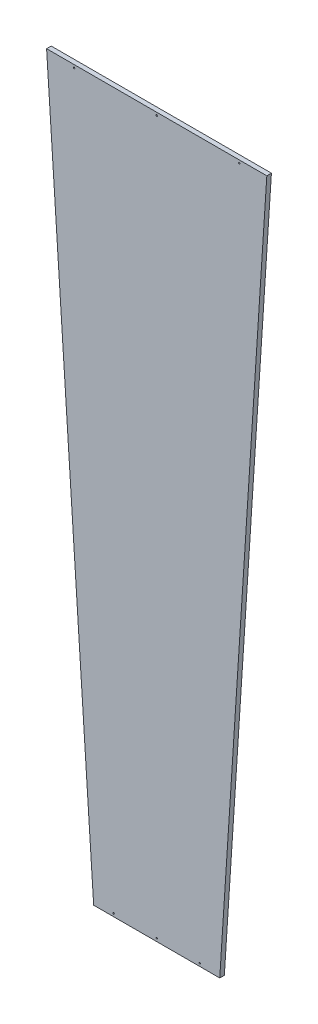
SolidWorks part; units mm, degrees
ref_plane "Plane1" through (0, 0, 0) normal (0, 0, 1) x (1, 0, 0)
ref_plane "Plane2" through (0, 0, 0) normal (0, 1, 0) x (1, 0, 0)
ref_plane "Plane3" through (0, 0, 0) normal (1, 0, 0) x (0, 0, -1)
ref_plane "Plane4" through (0, 0, 0) normal (0, 0, -1) x (-1, 0, 0)
sketch "Sketch1" plane through (0, 0, 0) normal (0, 0, -1) x (-1, 0, 0)
  line L0 (-4.387, 43.998) -> (4.387, 43.998)
  line L1 (0, 0) -> (6.16, 93.9841) construction
  line L2 (7.6633, 93.9841) -> (-7.6633, 93.9841)
  line L3 (-6.16, 93.9841) -> (0, 0) construction
  line L4 (7.5977, 92.9841) -> (-7.5977, 92.9841) construction
  line L5 (7.6633, 93.9841) -> (4.387, 43.998)
  line L6 (0, 121.6009) -> (0, 0) construction
  line L7 (-7.6633, 93.9841) -> (-4.387, 43.998)
  line L8 (4.4525, 44.998) -> (-4.4525, 44.998) construction
  dimension "D1" = 7.5
  dimension "D2" = 43.998
  dimension "D3" = 93.9841
  dimension "D4" = 1.5
  dimension "D5" = 49.9861
  dimension "D6" = 15.3265
  dimension "D7" = 8.774
  dimension "D8" = 1
  dimension "D9" = 1
extrude "Extrude1" add sketch "Sketch1" against normal mid plane 0.32
sketch "Sketch2" plane through (0, 0, 0.16) normal (0, 0, 1) x (1, 0, 0)
  line L0 (-1.3849, 42.3044) -> (-2.3441, 71.6034) construction
  line L1 (0, -55) -> (0, 55) construction
  line L2 (-5.4589, 44.8675) -> (2.5128, 45.1285) construction
  line L3 (4.387, 43.998) -> (-4.387, 43.998) construction
  line L4 (-2.7221, 44.9471) -> (-0.2234, 45.0289)
  line L5 (-2.7221, 44.9471) -> (-2.7227, 44.9671)
  line L6 (-0.2234, 45.0289) -> (-0.2241, 45.0489)
  line L7 (-2.7227, 44.9671) -> (-0.2241, 45.0489)
  point P5 (-1.4731, 44.998)
  dimension "D1" = 1.875
  dimension "D2" = 1
  dimension "D4" = 0.02
  dimension "D5" = 2.5
extrude "Extrude2" [suppressed] cut sketch "Sketch2" against normal blind 0.015
pattern_linear "LPattern1" [suppressed] count 65 spacing 0.075
sketch "Sketch3" [suppressed] plane through (0, 0, 0.16) normal (0, 0, 1) x (1, 0, 0)
  line L0 (-2.8795, 49.7565) -> (-2.8771, 49.6816) construction
  line L1 (-2.8799, 49.7665) -> (-2.8792, 49.7465) construction
  line L2 (-2.8774, 49.6916) -> (-2.8767, 49.6716) construction
  line L3 (-2.8783, 49.7191) -> (-4.7579, 49.6575) construction
  line L4 (-4.3871, 44) -> (-7.6958, 94.48) construction
sketch "Sketch4" plane through (0, 0, 0.16) normal (0, 0, 1) x (1, 0, 0)
  line L0 (0, 43.998) -> (0, 93.9841) construction
  line L1 (4.387, 43.998) -> (-4.387, 43.998) construction
  line L2 (-7.6633, 93.9841) -> (7.6633, 93.9841) construction
  line L3 (-10, 170.583) -> (-3, 44.198) construction
  circle A0 centre (-3, 44.198) radius 0.05
  circle A1 centre (0, 44.198) radius 0.05
  circle A2 centre (3, 44.198) radius 0.05
  circle A3 centre (-5.7464, 93.7841) radius 0.05
  circle A4 centre (0, 93.7841) radius 0.05
  circle A5 centre (5.7464, 93.7841) radius 0.05
  dimension "D1" = 0.2
  dimension "D4" = 0.2
  dimension "D5" = 0.1
  dimension "D2" = 3
  dimension "D6" = 10
  dimension "D7" = 126.585
extrude "Extrude3" cut sketch "Sketch4" against normal through all
